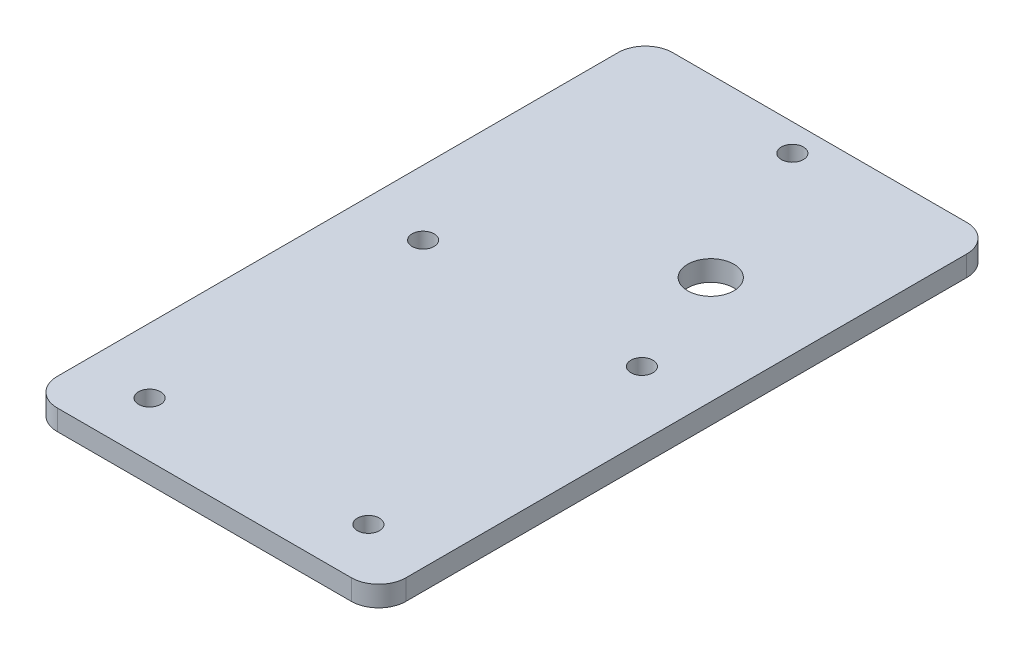
SolidWorks part; units mm, degrees
material "ABS"
ref_plane "Front Plane" through (0, 0, 0) normal (0, 0, 1) x (1, 0, 0)
ref_plane "Top Plane" through (0, 0, 0) normal (0, 1, 0) x (1, 0, 0)
ref_plane "Right Plane" through (0, 0, 0) normal (1, 0, 0) x (0, 0, -1)
sketch "Sketch2" plane through (0, 0, 0) normal (0, 1, 0) x (1, 0, 0)
  line L4 (-40.4812, 114.2369) -> (-40.4812, -15.9381)
  line L5 (-34.1312, -22.2881) -> (34.1313, -22.2881)
  line L6 (40.4813, -15.9381) -> (40.4813, 114.2369)
  line L7 (34.1313, 120.5869) -> (-34.1312, 120.5869)
  line L16 (-40.4812, 114.2369) -> (-40.4812, -15.9381)
  line L17 (-34.1312, -22.2881) -> (34.1313, -22.2881)
  line L18 (40.4813, -15.9381) -> (40.4813, 114.2369)
  line L19 (34.1313, 120.5869) -> (-34.1312, 120.5869)
  circle A0 centre (-25.4, -9.5881) radius 2.5527 construction
  circle A1 centre (25.4, -9.5881) radius 2.5527 construction
  circle A2 centre (25.4, 53.9119) radius 2.5527 construction
  circle A3 centre (-25.4, 53.9119) radius 2.5527 construction
  arc A4 (-40.4812, -15.9381) -> (-34.1312, -22.2881) centre (-34.1312, -15.9381) ccw
  arc A5 (34.1313, -22.2881) -> (40.4813, -15.9381) centre (34.1313, -15.9381) ccw
  arc A6 (40.4813, 114.2369) -> (34.1313, 120.5869) centre (34.1313, 114.2369) ccw
  arc A7 (-34.1312, 120.5869) -> (-40.4812, 114.2369) centre (-34.1312, 114.2369) ccw
  arc A12 (-40.4812, -15.9381) -> (-34.1312, -22.2881) centre (-34.1312, -15.9381) ccw
  arc A18 (34.1313, -22.2881) -> (40.4813, -15.9381) centre (34.1313, -15.9381) ccw
  arc A19 (40.4813, 114.2369) -> (34.1313, 120.5869) centre (34.1313, 114.2369) ccw
  arc A20 (-34.1312, 120.5869) -> (-40.4812, 114.2369) centre (-34.1312, 114.2369) ccw
  circle A21 centre (0, 114.2369) radius 2.5527 construction
  circle A26 centre (-25.4, -9.5881) radius 2.5527
  circle A27 centre (25.4, -9.5881) radius 2.5527
  circle A28 centre (25.4, 53.9119) radius 2.5527
  circle A29 centre (-25.4, 53.9119) radius 2.5527
  circle A30 centre (0, 114.2369) radius 2.5527
  dimension "D1" = 0
extrude "Boss-Extrude1" add sketch "Sketch2" against normal blind 4.7625
hole_wizard "1/2-13 Tapped Hole1" positions "Sketch3" profile "Sketch4" tap size "1/2-13" standard "ANSI Inch" end condition up to next
sketch "Sketch3" plane through (0, -4.7625, 0) normal (0, -1, 0) x (-1, 0, 0)
  line L14 (-21.8387, 76.1355) -> (-15.4998, 79.7953) construction
  line L15 (-4.1851, 45.5584) -> (-34.4426, 97.9661) construction
  line L16 (-15.4998, 79.7953) -> (-8.6216, 82.2987) construction
  line L17 (0, 58.6111) -> (-17.2432, 105.9863) construction
  point P41 (-15.4998, 79.7953)
  point P54 (-15.4998, 79.7953)
sketch "Sketch4" plane through (15.4998, -4.7625, -79.7953) normal (1, 0, 0) x (0, 0, -1)
  line L0 (0, 0) -> (0, 4.7625)
  line L1 (0, 4.7625) -> (5.3581, 4.7625)
  line L2 (5.3581, 4.7625) -> (5.3581, 0)
  line L5 (5.3581, 0) -> (0, 0)
  line L11 (0, -6.35) -> (0, 107.95) construction
  dimension "Thru Tap Drill Dia." = 10.7163
  dimension "Thru Tap Drill Depth" = 4.7625
cosmetic thread "Hole Thread1" parameters "D2"=12.7
sketch "Sketch5" plane through (0, -4.7625, 0) normal (0, -1, 0) x (-1, 0, 0)
  circle A0 centre (0, -3.0667) radius 0.7938
  circle A1 centre (-26.1938, 102.7286) radius 0.7937
  circle A2 centre (26.1937, 102.7286) radius 0.7937
  point P2 (-27.1183, 107.4523)
  point P10 (-26.1938, 102.7286)
  point P12 (26.1937, 102.7286)
  point P14 (0, -3.0667)
  dimension "D1" = 1.5875
extrude "Cut-Extrude1" cut sketch "Sketch5" against normal blind 0.762
sketch "Sketch6" plane through (0, -4.7625, 0) normal (0, -1, 0) x (1, 0, 0)
  line L0 (12.3192, -8.0202) -> (-17.3829, -8.0202) construction
  line L1 (36.1118, -91.4653) -> (4.3202, -91.4653) construction
  line L2 (-17.3829, -91.4653) -> (-40.1101, -91.4653) construction
  line L3 (24.481, -67.3013) -> (-17.3829, -67.3013) construction
  arc A0 (9.3917, -10.589) -> (-9.3916, -10.589) centre (0, 3.0667) ccw construction
  text T0 "4 - VENT INPUT"
  text T1 "5-PATIENT"
  text T2 "6-FILTER"
  text T3 "7-EXP. RATE"
  point P3 (12.3192, -8.0202)
  point P7 (0, 0)
  point P8 (29.4357, -111.6849)
  point P15 (28.4916, -90.1619)
  point P16 (36.1118, -91.4653)
  point P18 (21.9744, -64.1931)
  point P19 (26.7249, -112.2388)
  point P20 (24.481, -67.3013)
  point P21 (-19.0695, -91.4653)
  point P22 (-17.3829, -91.4653)
  point P23 (4.3202, -91.4653)
extrude "Cut-Extrude2" cut sketch "Sketch6" against normal blind 0.7874
